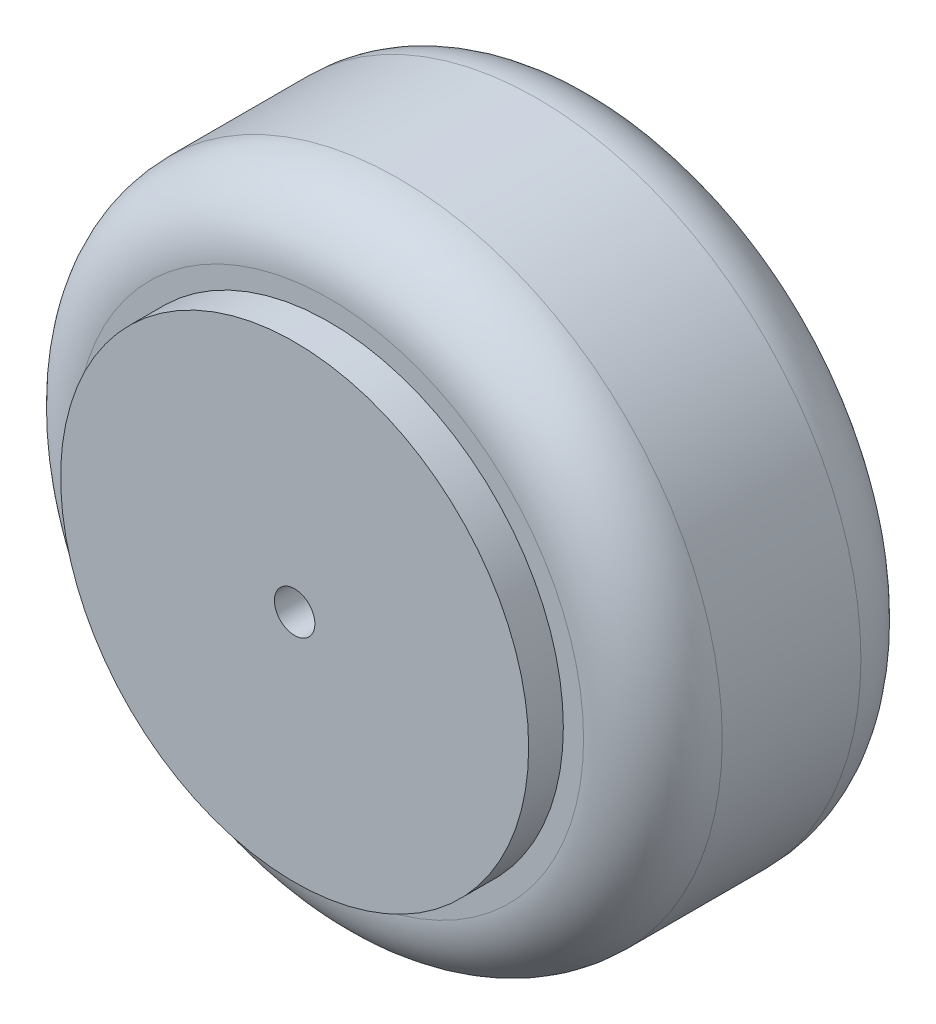
SolidWorks part; units mm, degrees
ref_plane "Front Plane" through (0, 0, 0) normal (0, 0, 1) x (1, 0, 0)
ref_plane "Top Plane" through (0, 0, 0) normal (0, 1, 0) x (1, 0, 0)
ref_plane "Right Plane" through (0, 0, 0) normal (1, 0, 0) x (0, 0, -1)
sketch "Sketch1" plane through (0, 0, 0) normal (0, 0, 1) x (1, 0, 0)
  circle A0 centre (0, 0) radius 40.5
  dimension "D1" = 81
extrude "Boss-Extrude1" add sketch "Sketch1" along normal blind 6 contours A0
sketch "Sketch2" plane through (0, 0, 0) normal (0, 1, 0) x (1, 0, 0)
  line L1 (56, 48) -> (16, 48)
  line L2 (56, 48) -> (56, 0)
  line L3 (56, 0) -> (16, 0)
  line L4 (16, 48) -> (16, 0)
  point P4 (36, 0)
  point P6 (16, 24)
  dimension "D1" = 48
  dimension "D2" = 40
  dimension "D3" = 36
  dimension "D4" = 24
ref_plane "Plane1" through (0, 0, -24) normal (0, 0, 1) x (1, 0, 0)
sketch "Sketch3" plane through (0, 0, -24) normal (0, 0, 1) x (1, 0, 0)
  circle A0 centre (0, 0) radius 70
  dimension "D1" = 140
sweep "Sweep1" add profiles "Sketch2" path "Sketch3"
fillet "Fillet1" radius 12 3 edges at (56, 0, 0) (16, 0, -48) (56, 0, -48)
sketch "Sketch4" plane through (0, 0, 0) normal (0, 0, -1) x (-1, 0, 0)
  circle A0 centre (0, 0) radius 16
extrude "Boss-Extrude2" add sketch "Sketch4" along normal blind 34
sketch "Sketch5" plane through (0, 0, -34) normal (0, 0, -1) x (-1, 0, 0)
  circle A0 centre (0, 0) radius 3.5
  dimension "D1" = 7
extrude "Cut-Extrude1" cut sketch "Sketch5" against normal through all and the other way through all
